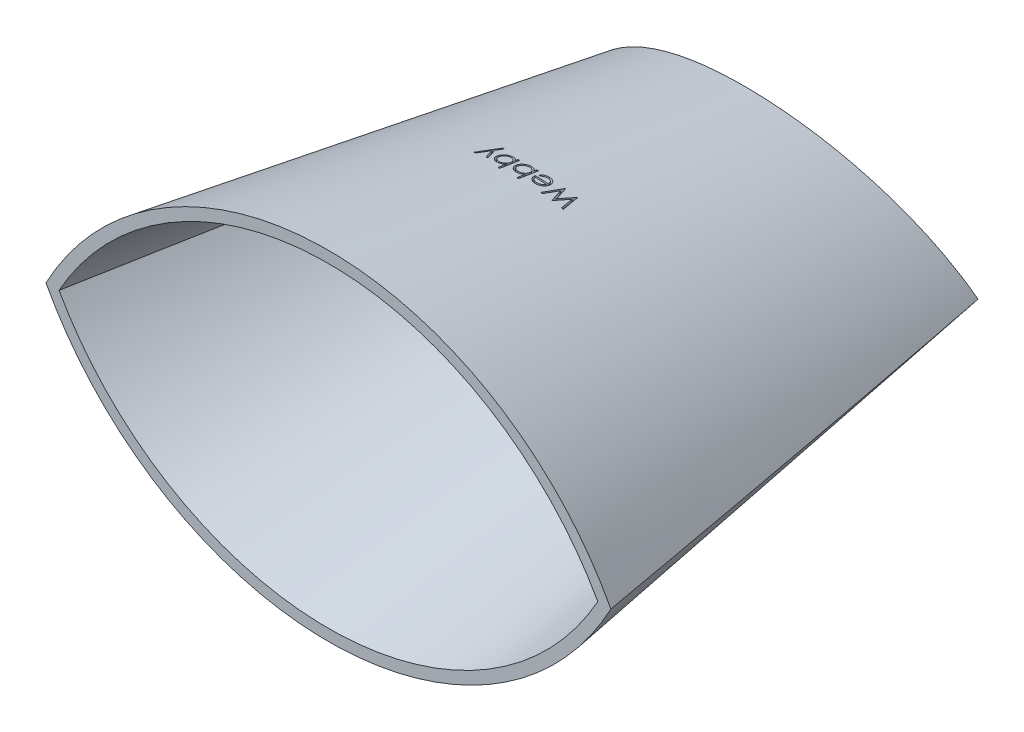
SolidWorks part; units mm, degrees
ref_plane "前基準面" through (0, 0, 0) normal (0, 0, 1) x (1, 0, 0)
ref_plane "上基準面" through (0, 0, 0) normal (0, 1, 0) x (1, 0, 0)
ref_plane "右基準面" through (0, 0, 0) normal (1, 0, 0) x (0, 0, -1)
sketch "草圖13" plane through (0, 0, 0) normal (0, 0, 1) x (1, 0, 0)
  line L2 (25.4007, 0) -> (-25.4007, 0) construction
  arc A4 (-50, 0) -> (50, 0) centre (0, -26.6667) cw
  arc A5 (-50, 0) -> (50, 0) centre (0, 26.6667) ccw
  point P6 (0, 30)
  dimension "D1" = 30
  dimension "D3" = 100
extrude "填料-伸長2" add sketch "草圖13" against normal blind 80 draft 9
sketch "草圖24" plane through (0, 0, 0) normal (0, 1, 0) x (1, 0, 0)
  line L0 (-34.9933, 80) -> (34.9933, 80)
  arc A0 (-34.9933, 80) -> (34.9933, 80) centre (0, 173.1907) ccw
extrude "除料-伸長3" cut sketch "草圖24" against normal mid plane 80
shell "薄殼4" thickness 2
sketch "草圖29" plane through (0, 0, 0) normal (1, 0, 0) x (0, 0, -1)
  line L0 (0, 30) -> (73.6502, 18.335) construction
  line L1 (0, 33) -> (0, -33) construction
  line L2 (73.6466, 18.3355) -> (0, 30) construction
ref_plane "平面2" through (0, 29.2658, -4.6353) normal (0, -0.9877, 0.1564) x (0, -0.1564, -0.9877)
sketch "草圖30" plane through (0, 29.2658, -4.6353) normal (0, -0.9877, 0.1564) x (0, -0.1564, -0.9877)
  line L0 (32.3405, 14.4733) -> (32.3405, -13.7176) construction
  text T0 "Webby"
extrude "除料-伸長4" cut sketch "草圖30" along normal blind 1
